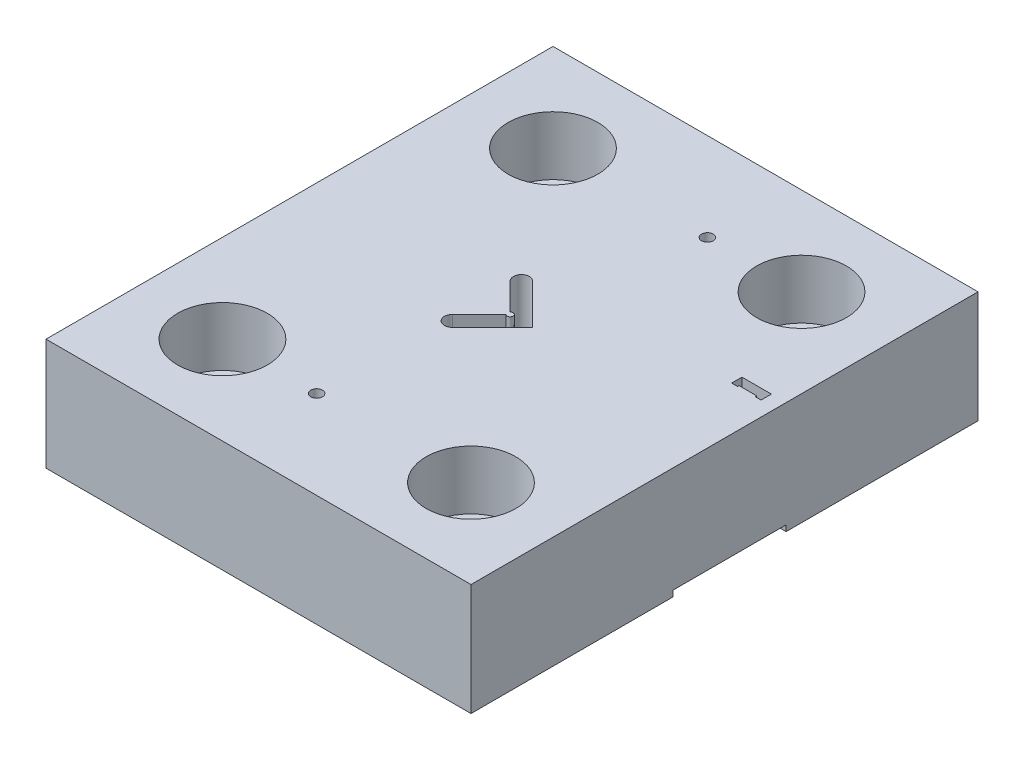
SolidWorks part; units mm, degrees
ref_plane "Front Plane" through (0, 0, 0) normal (0, 0, 1) x (1, 0, 0)
ref_plane "Top Plane" through (0, 0, 0) normal (0, 1, 0) x (1, 0, 0)
ref_plane "Right Plane" through (0, 0, 0) normal (1, 0, 0) x (0, 0, -1)
sketch "Sketch1" plane through (0, 0, 0) normal (0, 1, 0) x (1, 0, 0)
  line L1 (-72.25, -86.19) -> (72.25, -86.19)
  line L2 (-72.25, -86.19) -> (-72.25, 86.19)
  line L3 (-72.25, 86.19) -> (72.25, 86.19)
  line L4 (72.25, -86.19) -> (72.25, 86.19)
  line L5 (-72.25, -86.19) -> (72.25, 86.19) construction
  line L6 (-72.25, 86.19) -> (72.25, -86.19) construction
  point P0 (0, 0)
  dimension "D1" = 144.5
  dimension "D2" = 172.38
extrude "Boss-Extrude1" add sketch "Sketch1" along normal blind 38
sketch "Sketch2" plane through (0, 0, 0) normal (0, -1, 0) x (1, 0, 0)
  line L7 (-1.3339, -0.7071) -> (-10.4555, -9.8288)
  line L8 (-10.4555, 9.8288) -> (-1.3339, 0.7071)
  line L9 (7.01, 0) -> (-6.6372, 13.6472)
  line L10 (57.25, -20.94) -> (67.25, -20.94)
  line L11 (57.25, -17.44) -> (57.25, -20.94)
  line L12 (59.25, -17.44) -> (57.25, -17.44)
  line L13 (59.25, -17.94) -> (59.25, -17.44)
  line L14 (65.25, -17.94) -> (59.25, -17.94)
  line L15 (65.25, -17.44) -> (65.25, -17.94)
  line L16 (67.25, -17.44) -> (65.25, -17.44)
  line L17 (67.25, -20.94) -> (67.25, -17.44)
  line L18 (57.25, -20.94) -> (67.25, -20.94)
  line L19 (57.25, -17.44) -> (57.25, -20.94)
  line L20 (59.25, -17.44) -> (57.25, -17.44)
  line L21 (59.25, -17.94) -> (59.25, -17.44)
  line L22 (65.25, -17.94) -> (59.25, -17.94)
  line L23 (65.25, -17.44) -> (65.25, -17.94)
  line L24 (67.25, -17.44) -> (65.25, -17.44)
  line L25 (67.25, -20.94) -> (67.25, -17.44)
  line L26 (-6.6372, -13.6472) -> (7.01, 0)
  line L27 (-1.3339, -0.7071) -> (-10.4555, -9.8288)
  line L28 (-10.4555, 9.8288) -> (-1.3339, 0.7071)
  line L29 (7.01, 0) -> (-6.6372, 13.6472)
  line L30 (-6.6372, -13.6472) -> (7.01, 0)
  circle A0 centre (-42.25, -56.19) radius 10.5 construction
  circle A1 centre (10.25, -56.19) radius 1.99 construction
  circle A2 centre (42.25, -56.19) radius 10.5 construction
  circle A3 centre (-42.25, 56.19) radius 10.5 construction
  circle A4 centre (-10.25, 56.19) radius 1.99 construction
  circle A5 centre (42.25, 56.19) radius 10.5 construction
  circle A6 centre (-42.25, -56.19) radius 10.5
  circle A7 centre (10.25, -56.19) radius 1.99
  circle A8 centre (42.25, -56.19) radius 10.5
  circle A9 centre (-42.25, 56.19) radius 10.5
  circle A10 centre (-10.25, 56.19) radius 1.99
  circle A11 centre (42.25, 56.19) radius 10.5
  arc A15 (-10.4555, -9.8288) -> (-6.6372, -13.6472) centre (-8.5463, -11.738) ccw
  arc A16 (-1.3339, -0.7071) -> (-1.3339, 0.7071) centre (-0.6268, 0) ccw
  arc A17 (-6.6372, 13.6472) -> (-10.4555, 9.8288) centre (-8.5463, 11.738) ccw
  arc A18 (-10.4555, -9.8288) -> (-6.6372, -13.6472) centre (-8.5463, -11.738) ccw
  arc A19 (-1.3339, -0.7071) -> (-1.3339, 0.7071) centre (-0.6268, 0) ccw
  arc A20 (-6.6372, 13.6472) -> (-10.4555, 9.8288) centre (-8.5463, 11.738) ccw
  dimension "D1" = 0
  dimension "D2" = 0
extrude "Cut-Extrude1" cut sketch "Sketch2" against normal through all
sketch "Sketch3" plane through (0, 0, 0) normal (0, -1, 0) x (1, 0, 0)
  line L0 (-72.25, 17.44) -> (-72.25, -17.94) construction
  line L1 (-72.25, -17.94) -> (57.25, -17.94) construction
  line L2 (57.25, -17.94) -> (57.25, -20.94) construction
  line L3 (57.25, -20.94) -> (72.25, -20.94) construction
  line L4 (72.25, -32.6497) -> (72.25, -20.94) construction
  line L5 (72.25, 17.44) -> (72.25, -32.6497) construction
  line L6 (-72.25, 17.44) -> (72.25, 17.44) construction
  line L7 (-72.25, 17.44) -> (-72.25, -17.94)
  line L8 (-72.25, -17.94) -> (57.25, -17.94)
  line L9 (57.25, -17.94) -> (57.25, -20.94)
  line L10 (57.25, -20.94) -> (72.25, -20.94)
  line L11 (72.25, -32.6497) -> (72.25, -20.94)
  line L12 (72.25, 17.44) -> (72.25, -32.6497)
  line L13 (-72.25, 17.44) -> (72.25, 17.44)
  arc M6 (-6.6372, -13.6472) -> (-10.4555, -9.8288) centre (-8.5463, -11.738) cw
  line M7 (-10.4555, -9.8288) -> (-1.3339, -0.7071)
  arc M8 (-1.3339, -0.7071) -> (-1.3339, 0.7071) centre (-0.6268, 0) ccw
  line M9 (-1.3339, 0.7071) -> (-10.4555, 9.8288)
  arc M10 (-10.4555, 9.8288) -> (-6.6372, 13.6472) centre (-8.5463, 11.738) cw
  line M11 (-6.6372, 13.6472) -> (7.01, 0)
  line M12 (7.01, 0) -> (-6.6372, -13.6472)
  line M13 (67.25, -17.44) -> (67.25, -20.94)
  line M15 (57.25, -20.94) -> (57.25, -17.44)
  line M16 (57.25, -17.44) -> (59.25, -17.44)
  line M17 (59.25, -17.44) -> (59.25, -17.94)
  line M18 (59.25, -17.94) -> (65.25, -17.94)
  line M19 (65.25, -17.94) -> (65.25, -17.44)
  line M20 (65.25, -17.44) -> (67.25, -17.44)
  line M22 (72.25, -86.19) -> (72.25, 86.19)
  line M24 (-72.25, 86.19) -> (-72.25, -86.19)
extrude "Cut-Extrude2" cut sketch "Sketch3" against normal blind 2 contours L13 L8 L10 M24 M15 M16 M17 M18 M19 M20 M13 M22 M12 M6 M7 M8 M9 M10 M11
sketch "Sketch4" plane through (0, 38, 0) normal (0, 1, 0) x (1, 0, 0)
  circle A0 centre (-42.25, 56.19) radius 15.25
  circle A1 centre (42.25, 56.19) radius 15.25
  circle A2 centre (42.25, -56.19) radius 15.25
  circle A3 centre (-42.25, -56.19) radius 15.25
  dimension "D1" = 30.5
  dimension "D2" = 30.5
  dimension "D3" = 30.5
  dimension "D4" = 30.5
extrude "Cut-Extrude3" cut sketch "Sketch4" against normal blind 20
